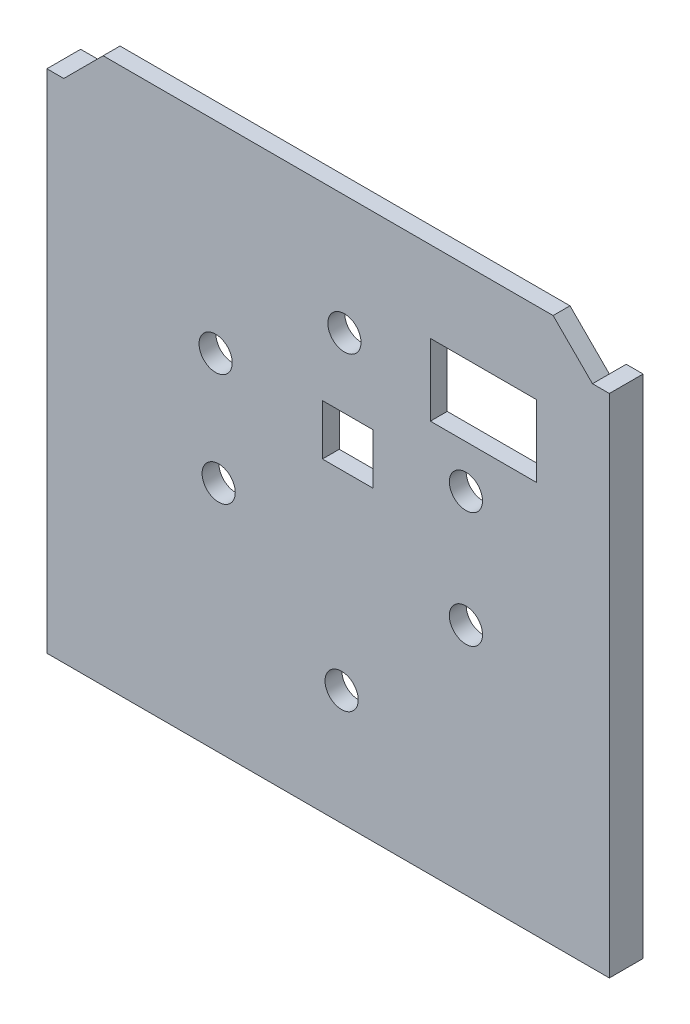
SolidWorks part; units mm, degrees
ref_plane "Alzado" through (0, 0, 0) normal (0, 0, 1) x (1, 0, 0)
ref_plane "Planta" through (0, 0, 0) normal (0, 1, 0) x (1, 0, 0)
ref_plane "Vista lateral" through (0, 0, 0) normal (1, 0, 0) x (0, 0, -1)
sketch "Croquis1" plane through (0, 0, -0.1563) normal (0, 0, 1) x (1, 0, 0)
  line L0 (51.2611, 62.9887) -> (44.2611, 69.9887)
  line L1 (-41.6389, 60.3887) -> (50.1611, 60.3887) construction
  line L2 (-41.6389, 60.3887) -> (-41.6389, -27.0113) construction
  line L3 (-41.6389, -27.0113) -> (50.1611, -27.0113) construction
  line L4 (50.1611, 60.3887) -> (50.1611, -27.0113) construction
  line L5 (3.2486, 27.3921) -> (12.2486, 27.3921)
  line L6 (3.2486, 27.3921) -> (3.2486, 36.3921)
  line L7 (3.2486, 36.3921) -> (12.2486, 36.3921)
  line L8 (12.2486, 27.3921) -> (12.2486, 36.3921)
  line L9 (22.4361, 55.5637) -> (41.2861, 55.5637)
  line L10 (22.4361, 55.5637) -> (22.4361, 42.8137)
  line L11 (22.4361, 42.8137) -> (41.2861, 42.8137)
  line L12 (41.2861, 55.5637) -> (41.2861, 42.8137)
  line L14 (-45.7389, 62.9887) -> (-45.7389, -27.0113)
  line L15 (-45.7389, -27.0113) -> (54.2611, -27.0113)
  line L16 (54.2611, 62.9887) -> (54.2611, -27.0113)
  line L17 (-35.7389, 69.9887) -> (44.2611, 69.9887)
  line L18 (-42.7389, 62.9887) -> (-35.7389, 69.9887)
  line L19 (51.2611, 62.9887) -> (54.2611, 62.9887)
  line L20 (-42.7389, 62.9887) -> (-45.7389, 62.9887)
  circle A0 centre (7.1611, 48.7704) radius 2.95
  circle A1 centre (28.7611, 35.1704) radius 2.95
  circle A2 centre (28.7611, 14.5704) radius 2.95
  circle A3 centre (6.6611, -6.5296) radius 2.95
  circle A4 centre (-15.1989, 14.4704) radius 2.95
  circle A5 centre (-15.7389, 34.1704) radius 2.95
  dimension "D1" = 5.9
  dimension "D2" = 100
  dimension "D3" = 90
  dimension "D4" = 3
  dimension "D5" = 3
  dimension "D6" = 7
  dimension "D7" = 135
  dimension "D8" = 135
extrude "Saliente-Extruir1" add sketch "Croquis1" along normal blind 3
sketch "Croquis9" plane through (0, 0, -0.1563) normal (0, 0, -1) x (-1, 0, 0)
  line L0 (-54.2611, 62.9887) -> (-51.2611, 62.9887)
  line L1 (-51.2611, 62.9887) -> (-51.2611, -24.0113)
  line L2 (-51.2611, -24.0113) -> (42.7389, -24.0113)
  line L3 (42.7389, -24.0113) -> (42.7389, 62.9887)
  line L4 (42.7389, 62.9887) -> (45.7389, 62.9887) construction
  line L5 (42.7389, 62.9887) -> (45.7389, 62.9887)
  line L6 (45.7389, 62.9887) -> (45.7389, -27.0113)
  line L7 (45.7389, -27.0113) -> (-54.2611, -27.0113)
  line L8 (45.7389, -27.0113) -> (-54.2611, -27.0113) construction
  line L9 (-54.2611, -27.0113) -> (-54.2611, 62.9887) construction
  line L10 (-54.2611, -27.0113) -> (-54.2611, 62.9887)
  dimension "D1" = 3
  dimension "D2" = 3
extrude "Saliente-Extruir6" add sketch "Croquis9" along normal blind 3
